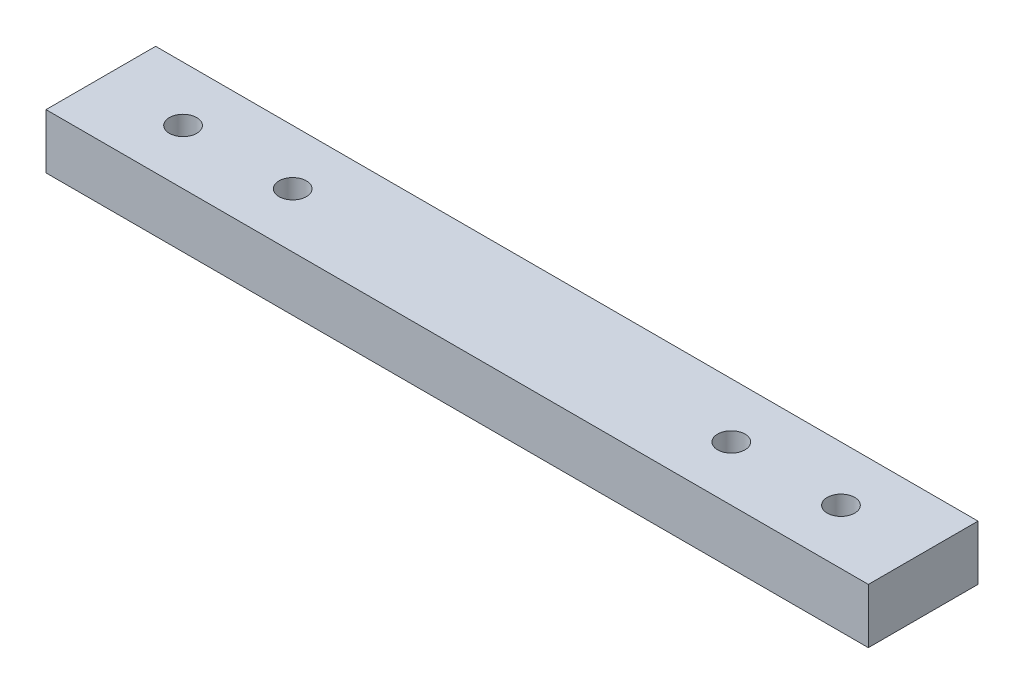
SolidWorks part; units mm, degrees
ref_plane "Front Plane" through (0, 0, 0) normal (0, 0, 1) x (1, 0, 0)
ref_plane "Top Plane" through (0, 0, 0) normal (0, 1, 0) x (1, 0, 0)
ref_plane "Right Plane" through (0, 0, 0) normal (1, 0, 0) x (0, 0, -1)
sketch "Sketch1" plane through (0, 0, 0) normal (0, 1, 0) x (1, 0, 0)
  line L1 (0, 0) -> (150, 0)
  line L2 (0, 0) -> (0, 20)
  line L3 (0, 20) -> (150, 20)
  line L4 (150, 0) -> (150, 20)
  circle A0 centre (15, 10) radius 2.5
  circle A1 centre (35, 10) radius 2.5
  circle A2 centre (115, 10) radius 2.5
  circle A3 centre (135, 10) radius 2.5
  dimension "D3" = 5
  dimension "D4" = 5
  dimension "D5" = 5
  dimension "D6" = 5
  dimension "D1" = 150
  dimension "D2" = 20
  dimension "D7" = 20
  dimension "D8" = 20
  dimension "D9" = 15
  dimension "D10" = 10
  dimension "D11" = 10
  dimension "D12" = 15
  dimension "D13" = 10
  dimension "D14" = 10
extrude "Boss-Extrude1" add sketch "Sketch1" along normal blind 10
